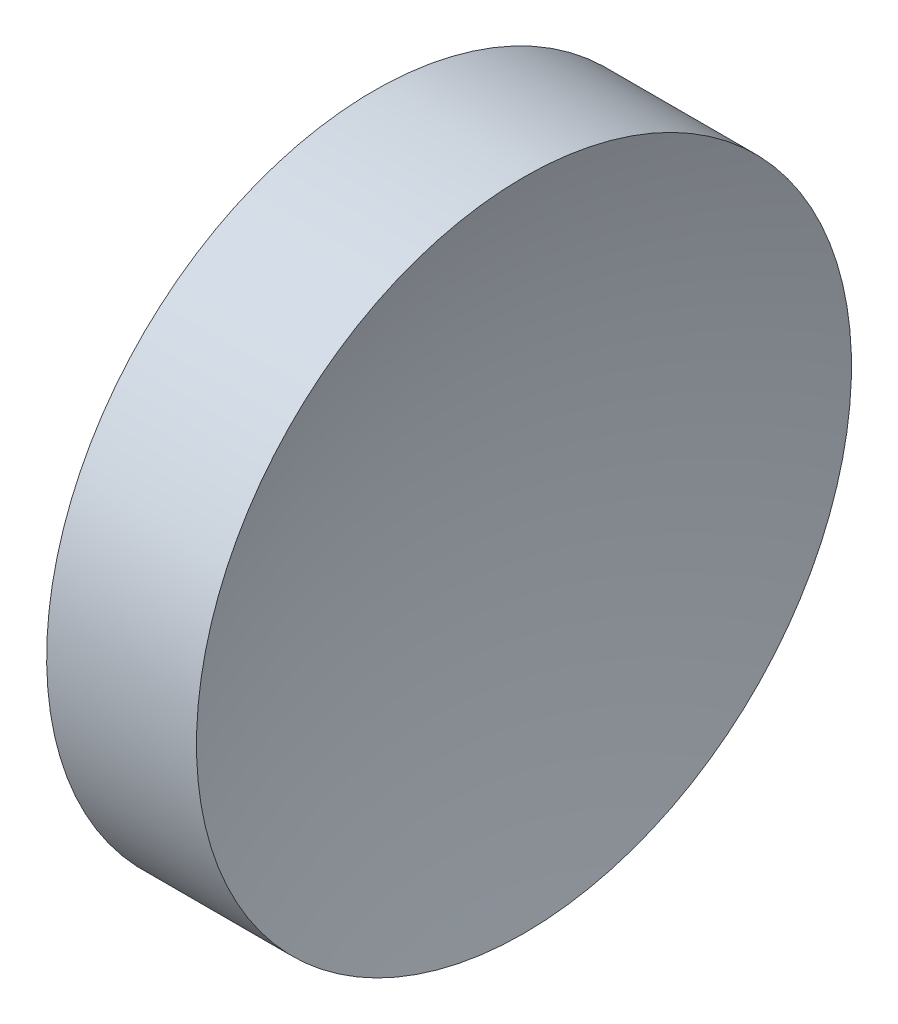
SolidWorks part; units mm, degrees
ref_plane "前视基准面" through (0, 0, 0) normal (0, 0, 1) x (1, 0, 0)
ref_plane "上视基准面" through (0, 0, 0) normal (0, 1, 0) x (1, 0, 0)
ref_plane "右视基准面" through (0, 0, 0) normal (1, 0, 0) x (0, 0, -1)
sketch "草图1" plane through (0, 0, 0) normal (0, 0, 1) x (1, 0, 0)
  line L0 (21.506, 13.0311) -> (26.997, 13.0311) construction
  line L1 (22.4242, 13.0311) -> (22.4242, 18.0311)
  line L2 (22.4242, 18.0311) -> (24.7116, 18.0311)
  line L3 (23.9242, 13.0311) -> (22.4242, 13.0311)
  arc A0 (24.7116, 18.0311) -> (23.9242, 13.0311) centre (40.1942, 13.0311) ccw
revolve "旋转1" add sketch "草图1" angle 360 about L0
